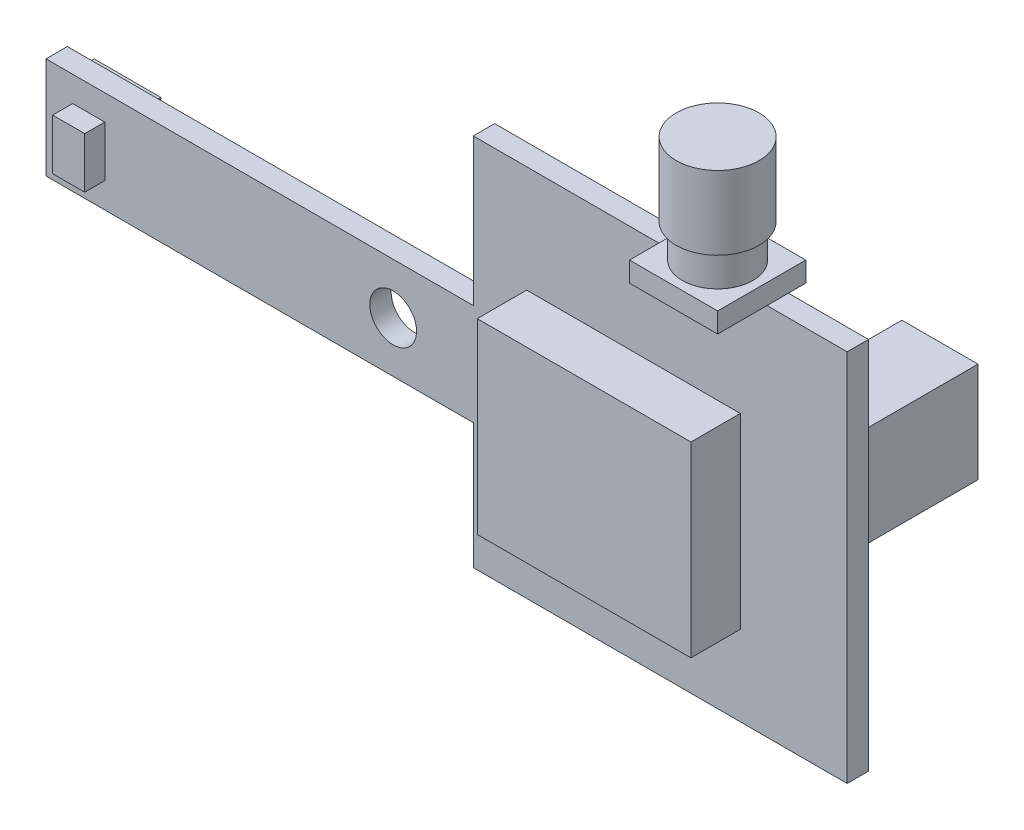
SolidWorks part; units mm, degrees
ref_plane "Front Plane" through (0, 0, 0) normal (0, 0, 1) x (1, 0, 0)
ref_plane "Top Plane" through (0, 0, 0) normal (0, 1, 0) x (1, 0, 0)
ref_plane "Right Plane" through (0, 0, 0) normal (1, 0, 0) x (0, 0, -1)
sketch "Sketch1" plane through (0, 0, 0) normal (0, 0, 1) x (1, 0, 0)
  line L0 (0, 0) -> (-6, 0) construction
  line L1 (0, 14.8) -> (28, 14.8)
  line L3 (0, -13.2) -> (28, -13.2)
  line L4 (28, 14.8) -> (28, -13.2)
  line L5 (-32, 3.8) -> (0, 3.8)
  line L6 (-32, 3.8) -> (-32, -3.8)
  line L7 (-32, -3.8) -> (0, -3.8)
  line L8 (0, 3.8) -> (0, -3.8)
  line L9 (0, 14.8) -> (0, -13.2)
  circle A0 centre (-6, 0) radius 1.75
  point P4 (0, 0)
  point P10 (0, 0)
  point P14 (0, 0)
  dimension "D5" = 3.5
  dimension "D1" = 28
  dimension "D2" = 28
  dimension "D3" = 7.6
  dimension "D4" = 60
  dimension "D6" = 26
  dimension "D7" = 34
  dimension "D8" = 11
  dimension "D9" = 9.4
extrude "Boss-Extrude1" add sketch "Sketch1" along normal blind 1.6
sketch "Sketch2" plane through (0, 14.8, 0) normal (0, 1, 0) x (1, 0, 0)
  line L0 (28, -1.6) -> (28, 0) construction
  line L1 (15.4, 1.3) -> (22, 1.3)
  line L2 (15.4, 1.3) -> (15.4, -5.3)
  line L3 (15.4, -5.3) -> (22, -5.3)
  line L4 (22, 1.3) -> (22, -5.3)
  line L5 (0, -1.6) -> (0, 0) construction
  line L6 (0, -1.6) -> (28, -1.6) construction
  line L8 (0, 0) -> (28, 0) construction
  point P6 (28, -0.8)
  dimension "D1" = 6.6
  dimension "D2" = 6.6
  dimension "D3" = 6
  dimension "D4" = 15.4
  dimension "D5" = 2.9
  dimension "D6" = 5.3
extrude "Boss-Extrude2" add sketch "Sketch2" along normal blind 1.5 separate body
sketch "Sketch3" plane through (0, 16.3, 0) normal (0, 1, 0) x (1, 0, 0)
  line L0 (15.4, 1.3) -> (22, -5.3) construction
  circle A0 centre (18.7, -2) radius 2.65
  dimension "D1" = 5.3
extrude "Boss-Extrude3" add sketch "Sketch3" along normal blind 2.5
sketch "Sketch4" plane through (0, 18.8, 0) normal (0, 1, 0) x (1, 0, 0)
  circle A0 centre (18.7, -2) radius 3.1
  dimension "D1" = 6.2
extrude "Boss-Extrude4" add sketch "Sketch4" along normal blind 5.5
sketch "Sketch5" plane through (0, 0, 1.6) normal (0, 0, 1) x (1, 0, 0)
  line L0 (0, -13.2) -> (28, -13.2) construction
  line L1 (4, 6.8) -> (20, 6.8)
  line L2 (4, 6.8) -> (4, -7.2)
  line L3 (4, -7.2) -> (20, -7.2)
  line L4 (20, 6.8) -> (20, -7.2)
  line L5 (0, 14.8) -> (28, 14.8) construction
  line L6 (0, -3.8) -> (0, -13.2) construction
  line L7 (28, 14.8) -> (28, -13.2) construction
  dimension "D1" = 16
  dimension "D2" = 14
  dimension "D3" = 20
  dimension "D4" = 22
  dimension "D5" = 20
  dimension "D6" = 24
extrude "Boss-Extrude5" add sketch "Sketch5" along normal up to surface (3.7 mm away) separate body up to face at (18.7, 15.55, 5.3)
sketch "Sketch6" plane through (0, 0, 1.6) normal (0, 0, 1) x (1, 0, 0)
  line L0 (-32, 3.8) -> (0, 3.8) construction
  line L1 (-30, 1.9) -> (-27.6, 1.9)
  line L2 (-30, 1.9) -> (-30, -1.9)
  line L3 (-30, -1.9) -> (-27.6, -1.9)
  line L4 (-27.6, 1.9) -> (-27.6, -1.9)
  line L5 (-32, -3.8) -> (0, -3.8) construction
  line L6 (-32, 3.8) -> (-32, -3.8) construction
  line L7 (28, 14.8) -> (28, -13.2) construction
  dimension "D1" = 2.4
  dimension "D2" = 3.8
  dimension "D3" = 5.7
  dimension "D4" = 5.7
  dimension "D5" = 4.4
  dimension "D6" = 58
extrude "Boss-Extrude6" add sketch "Sketch6" along normal blind 1.5 separate body
sketch "Sketch7" plane through (0, 0, 0) normal (0, 0, -1) x (-1, 0, 0)
  line L0 (32, 3.8) -> (32, -3.8) construction
  line L1 (-26.7, 7.8) -> (-21, 7.8)
  line L2 (-26.7, 7.8) -> (-26.7, 0.3)
  line L3 (-26.7, 0.3) -> (-21, 0.3)
  line L4 (-21, 7.8) -> (-21, 0.3)
  line L5 (-12.7, 3.6) -> (-5.4, 3.6)
  line L6 (-12.7, 3.6) -> (-12.7, -3.2)
  line L7 (-12.7, -3.2) -> (-5.4, -3.2)
  line L8 (-5.4, 3.6) -> (-5.4, -3.2)
  line L9 (26.5, 2.5) -> (31.5, 2.5)
  line L10 (26.5, 2.5) -> (26.5, -2.5)
  line L11 (26.5, -2.5) -> (31.5, -2.5)
  line L12 (31.5, 2.5) -> (31.5, -2.5)
  line L13 (32, 3.8) -> (0, 3.8) construction
  line L14 (32, -3.8) -> (0, -3.8) construction
  line L15 (0, 14.8) -> (-28, 14.8) construction
  line L16 (0, -13.2) -> (-28, -13.2) construction
  line L17 (-28, 14.8) -> (-28, -13.2) construction
  line L18 (0, -3.8) -> (0, -13.2) construction
  dimension "D1" = 5
  dimension "D2" = 5
  dimension "D3" = 5.5
  dimension "D4" = 6.3
  dimension "D5" = 6.3
  dimension "D6" = 7.3
  dimension "D7" = 6.8
  dimension "D8" = 18
  dimension "D9" = 16.8
  dimension "D10" = 22.6
  dimension "D11" = 12.7
  dimension "D12" = 5.7
  dimension "D13" = 7.5
  dimension "D14" = 7
  dimension "D15" = 21
  dimension "D16" = 14.5
extrude "Boss-Extrude7" add sketch "Sketch7" along normal blind 1.5 separate body
other "Move Face2" face at (23.85, 4.05, -1.5) parameters "D1"=8
